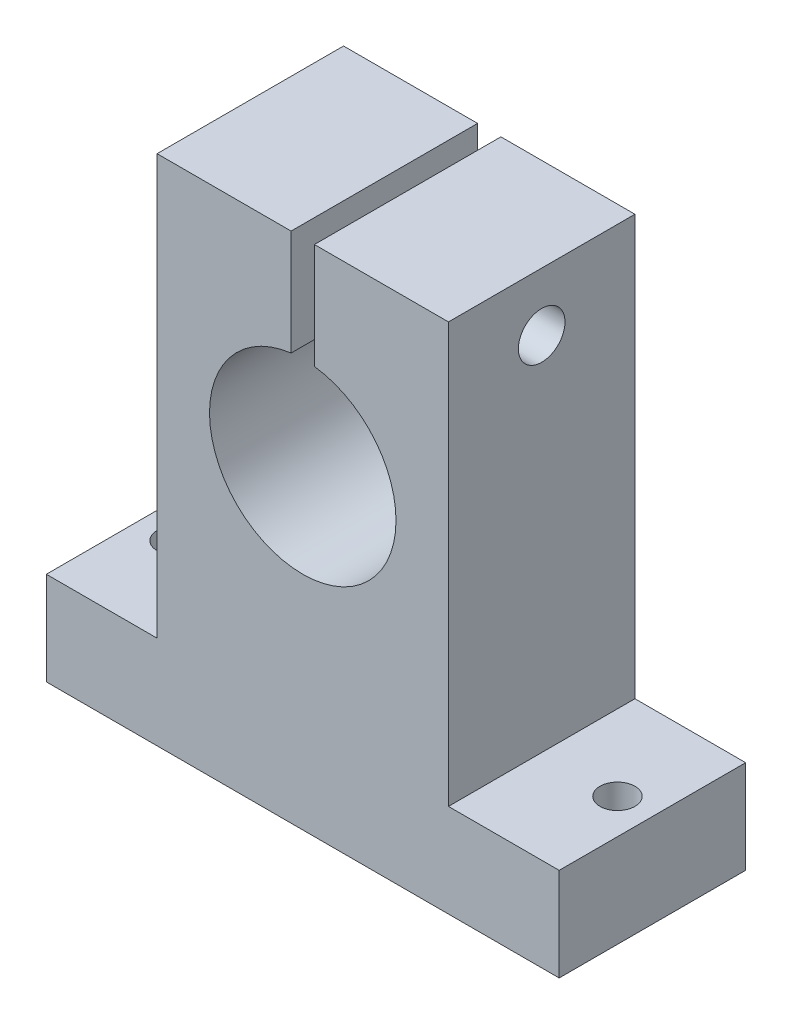
SolidWorks part; units mm, degrees
ref_plane "前视基准面" through (0, 0, 0) normal (0, 0, 1) x (1, 0, 0)
ref_plane "上视基准面" through (0, 0, 0) normal (0, 1, 0) x (1, 0, 0)
ref_plane "右视基准面" through (0, 0, 0) normal (1, 0, 0) x (0, 0, -1)
sketch "草图1" plane through (0, 0, 0) normal (0, 0, 1) x (1, 0, 0)
  line L0 (-24.9217, 3.1233) -> (19.0783, 3.1233)
  line L1 (19.0783, 3.1233) -> (19.0783, 11.1233)
  line L2 (19.0783, 11.1233) -> (9.5783, 11.1233)
  line L3 (9.5783, 11.1233) -> (9.5783, 47.1233)
  line L4 (9.5783, 47.1233) -> (-15.4217, 47.1233)
  line L5 (-15.4217, 47.1233) -> (-15.4217, 11.1233)
  line L6 (-15.4217, 11.1233) -> (-24.9217, 11.1233)
  line L7 (-24.9217, 11.1233) -> (-24.9217, 3.1233)
  line L8 (-2.9217, 3.1233) -> (-2.9217, 30.1233) construction
  circle A0 centre (-2.9217, 30.1233) radius 8
  dimension "D7" = 16
  dimension "D1" = 44
  dimension "D2" = 8
  dimension "D3" = 9.5
  dimension "D4" = 36
  dimension "D5" = 25
  dimension "D6" = 27
extrude "凸台-拉伸1" add sketch "草图1" along normal blind 16
sketch "草图2" plane through (0, 47.1233, 0) normal (0, 1, 0) x (1, 0, 0)
  line L0 (-2.9217, -16) -> (-2.9217, 0) construction
  line L1 (9.5783, -16) -> (-15.4217, -16) construction
  line L2 (9.5783, 0) -> (-15.4217, 0) construction
  line L4 (-3.9217, 0) -> (-3.9217, -16)
  line L5 (-3.9217, -16) -> (-1.9217, -16)
  line L6 (-1.9217, -16) -> (-1.9217, 0)
  line L7 (-1.9217, 0) -> (-3.9217, 0)
  dimension "D1" = 1
  dimension "D2" = 2
extrude "切除-拉伸1" cut sketch "草图2" against normal blind 16
sketch "草图3" plane through (9.5783, 0, 0) normal (1, 0, 0) x (0, 0, -1)
  line L0 (-8, 47.1233) -> (-8, 42.1233) construction
  line L1 (-16, 47.1233) -> (0, 47.1233) construction
  circle A0 centre (-8, 42.1233) radius 2
  dimension "D2" = 4
  dimension "D1" = 5
extrude "切除-拉伸2" cut sketch "草图3" against normal blind 39
sketch "草图4" plane through (0, 3.1233, 0) normal (0, -1, 0) x (1, 0, 0)
  line L0 (-2.9217, 16) -> (-2.9217, 0) construction
  line L1 (-24.9217, 16) -> (19.0783, 16) construction
  line L2 (-24.9217, 0) -> (19.0783, 0) construction
  line L3 (-2.9217, 8) -> (-21.9217, 8) construction
  line L4 (-2.9217, 8) -> (16.0783, 8) construction
  circle A0 centre (-21.9217, 8) radius 1.5
  circle A1 centre (16.0783, 8) radius 1.5
  dimension "D3" = 3
  dimension "D4" = 3
  dimension "D1" = 19
  dimension "D2" = 19
extrude "切除-拉伸3" cut sketch "草图4" against normal blind 39
